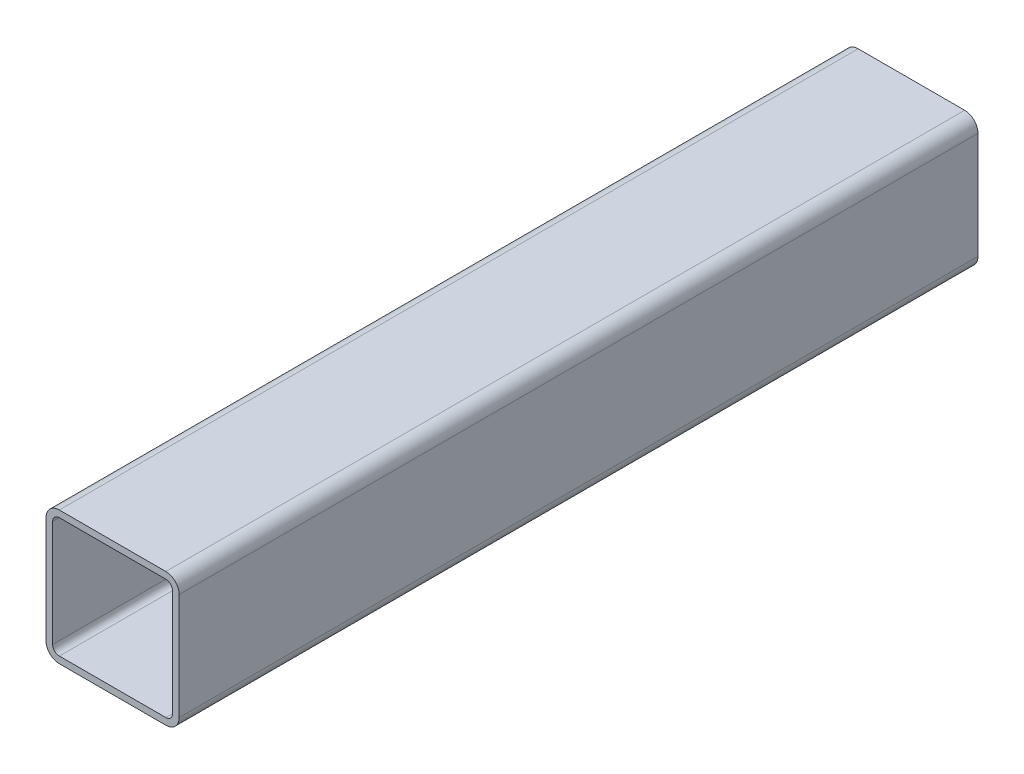
SolidWorks part; units mm, degrees
material "1.0116 (S235J2G3)"
ref_plane "Front Plane" through (0, 0, 0) normal (0, 0, 1) x (1, 0, 0)
ref_plane "Top Plane" through (0, 0, 0) normal (0, 1, 0) x (1, 0, 0)
ref_plane "Right Plane" through (0, 0, 0) normal (1, 0, 0) x (0, 0, -1)
sketch "Sketch2" plane through (0, 0, 0) normal (0, 0, 1) x (1, 0, 0)
  line L0 (-50, 40) -> (-50, -40)
  line L1 (-40, -50) -> (40, -50)
  line L2 (50, -40) -> (50, 40)
  line L3 (40, 50) -> (-40, 50)
  line L8 (0, 0) -> (50, 0) construction
  line L9 (0, 0) -> (0, 50) construction
  line L10 (40, 45) -> (-40, 45)
  line L11 (-45, 40) -> (-45, -40)
  line L12 (-40, -45) -> (40, -45)
  line L13 (45, -40) -> (45, 40)
  arc A0 (-40, 50) -> (-50, 40) centre (-40, 40) ccw
  arc A1 (-50, -40) -> (-40, -50) centre (-40, -40) ccw
  arc A2 (40, -50) -> (50, -40) centre (40, -40) ccw
  arc A3 (50, 40) -> (40, 50) centre (40, 40) ccw
  arc A4 (-40, 45) -> (-45, 40) centre (-40, 40) ccw
  arc A5 (-45, -40) -> (-40, -45) centre (-40, -40) ccw
  arc A6 (40, -45) -> (45, -40) centre (40, -40) ccw
  arc A7 (45, 40) -> (40, 45) centre (40, 40) ccw
  point P15 (0, 50)
  point P18 (50, 0)
  point P24 (0, 0)
  dimension "D7" = 10
  dimension "D1" = 100
  dimension "D2" = 100
  dimension "D3" = 5
extrude "Boss-Extrude1" add sketch "Sketch2" along normal mid plane 600
